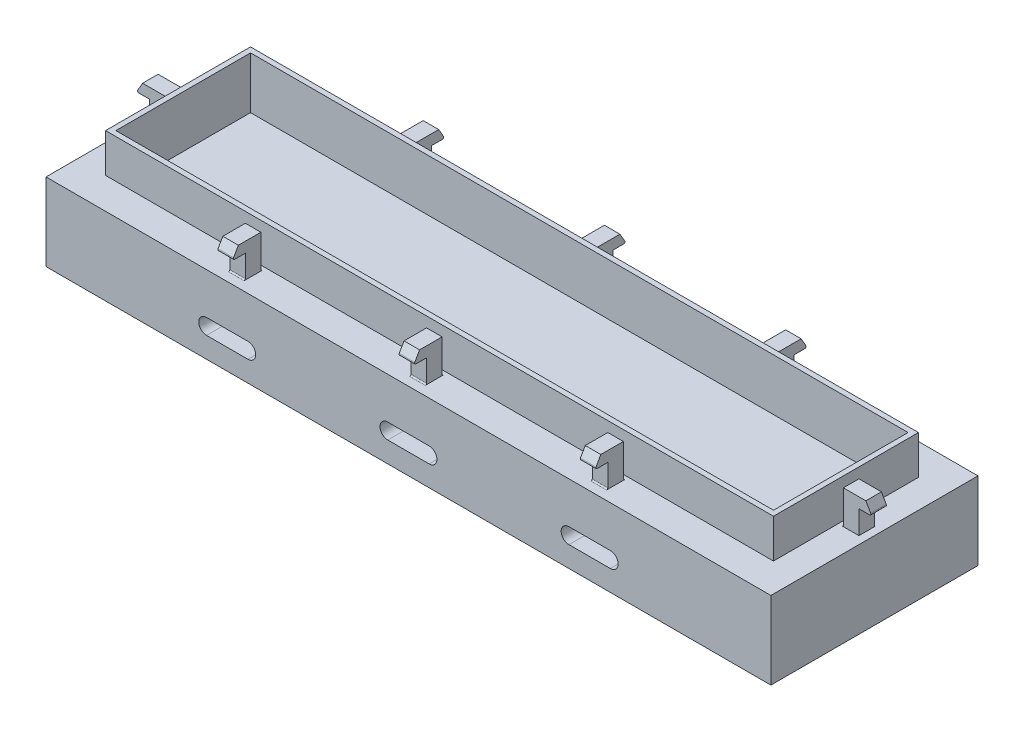
SolidWorks part; units mm, degrees
ref_plane "Front Plane" through (0, 0, 0) normal (0, 0, 1) x (1, 0, 0)
ref_plane "Top Plane" through (0, 0, 0) normal (0, 1, 0) x (1, 0, 0)
ref_plane "Right Plane" through (0, 0, 0) normal (1, 0, 0) x (0, 0, -1)
sketch "Sketch1" plane through (0, 0, 0) normal (0, 1, 0) x (1, 0, 0)
  line L1 (-70, -20) -> (70, -20)
  line L2 (-70, -20) -> (-70, 20)
  line L3 (-70, 20) -> (70, 20)
  line L4 (70, -20) -> (70, 20)
  line L5 (-70, -20) -> (70, 20) construction
  line L6 (-70, 20) -> (70, -20) construction
  point P0 (0, 0)
  dimension "D1" = 40
  dimension "D2" = 140
extrude "Boss-Extrude1" add sketch "Sketch1" along normal blind 15
ref_plane "Plane1" through (-35, 0, 0) normal (1, 0, 0) x (0, 0, -1)
sketch "Sketch3" plane through (0, 0, 0) normal (0, 0, 1) x (1, 0, 0)
  line L0 (-65.5, 15) -> (-65.5, 21.5)
  line L1 (-65.5, 21.5) -> (-69.8453, 21.5)
  line L2 (-69.8453, 21.5) -> (-71, 19.5)
  line L3 (-71, 19.5) -> (-68.5, 19.5)
  line L4 (-68.5, 19.5) -> (-68.5, 15)
  line L5 (-68.5, 15) -> (-65.5, 15)
  line L7 (-70, 15) -> (70, 15) construction
  line L8 (-70, 15) -> (-70, 0) construction
  dimension "D1" = 3
  dimension "D2" = 2.5
  dimension "D3" = 6.5
  dimension "D4" = 4.5
  dimension "D5" = 60
  dimension "D6" = 1.5
sketch "Sketch6" plane through (0, 0, 0) normal (1, 0, 0) x (0, 0, -1)
  line L0 (-15, 15) -> (-15, 21.5)
  line L1 (-15, 21.5) -> (-19.3453, 21.5)
  line L2 (-19.3453, 21.5) -> (-20.5, 19.5)
  line L3 (-20.5, 19.5) -> (-18, 19.5)
  line L4 (-18, 19.5) -> (-18, 15)
  line L5 (-18, 15) -> (-15, 15)
  line L6 (-20, 15) -> (20, 15) construction
  line L7 (-20, 15) -> (-20, 0) construction
  dimension "D1" = 3
  dimension "D2" = 2.5
  dimension "D3" = 6.5
  dimension "D4" = 4.5
  dimension "D5" = 60
  dimension "D6" = 2
sketch "Sketch7" plane through (-35, 0, 0) normal (1, 0, 0) x (0, 0, -1)
  line L0 (-15, 15) -> (-15, 21.5)
  line L1 (-15, 21.5) -> (-19.3453, 21.5)
  line L2 (-19.3453, 21.5) -> (-20.5, 19.5)
  line L3 (-20.5, 19.5) -> (-18, 19.5)
  line L4 (-18, 19.5) -> (-18, 15)
  line L5 (-18, 15) -> (-15, 15)
  line L6 (-20, 15) -> (20, 15) construction
  line L7 (-20, 15) -> (-20, 0) construction
  dimension "D1" = 3
  dimension "D2" = 2.5
  dimension "D3" = 6.5
  dimension "D4" = 4.5
  dimension "D5" = 60
  dimension "D6" = 2
extrude "Boss-Extrude2" add sketch "Sketch3" along normal blind 1.5 and the other way blind 1.5
extrude "Boss-Extrude3" add sketch "Sketch6" against normal blind 1.5
extrude "Boss-Extrude4" add sketch "Sketch7" along normal blind 1.5 and the other way blind 1.5
fillet "Fillet2" radius 0.25 1 edges at (-71, 19.5, 0)
mirror "Mirror9" about plane through (0, 0, 0) normal (1, 0, 0) of "Boss-Extrude3"
mirror "Mirror10" about plane through (0, 0, 0) normal (0, 0, 1) of "Boss-Extrude4", "Mirror9", "Boss-Extrude3"
mirror "Mirror11" about plane through (0, 0, 0) normal (1, 0, 0) of "Boss-Extrude2", "Mirror10", "Boss-Extrude4"
sketch "Sketch2" plane through (0, 15, 0) normal (0, 1, 0) x (1, 0, 0)
  line L1 (-64.5, -14) -> (64.5, -14)
  line L2 (-64.5, -14) -> (-64.5, 14)
  line L3 (-64.5, 14) -> (64.5, 14)
  line L4 (64.5, -14) -> (64.5, 14)
  line L5 (-64.5, -14) -> (64.5, 14) construction
  line L6 (-64.5, 14) -> (64.5, -14) construction
  line L8 (1.5, 15) -> (-1.5, 15) construction
  line L9 (-65.5, 1.5) -> (-65.5, -1.5) construction
  point P0 (0, 0)
  dimension "D1" = 1
  dimension "D2" = 1
extrude "Boss-Extrude5" add sketch "Sketch2" along normal blind 7.5
sketch "Sketch8" plane through (0, 22.5, 0) normal (0, 1, 0) x (1, 0, 0)
  line L0 (64.5, 14) -> (-64.5, 14) construction
  line L1 (-63.5, -13) -> (63.5, -13)
  line L2 (-63.5, -13) -> (-63.5, 13)
  line L3 (-63.5, 13) -> (63.5, 13)
  line L4 (63.5, -13) -> (63.5, 13)
  line L5 (-63.5, -13) -> (63.5, 13) construction
  line L6 (-63.5, 13) -> (63.5, -13) construction
  line L7 (-64.5, 14) -> (-64.5, -14) construction
  point P0 (0, 0)
  point P8 (0, 14)
  point P11 (-64.5, 0)
  dimension "D1" = 1
  dimension "D2" = 1
extrude "Cut-Extrude1" cut sketch "Sketch8" against normal blind 10
sketch "Sketch9" plane through (0, 0, 20) normal (0, 0, 1) x (1, 0, 0)
  line L0 (-4, 5.5) -> (4, 5.5) construction
  line L1 (-4, 7) -> (4, 7)
  line L2 (-4, 4) -> (4, 4)
  arc A0 (-4, 7) -> (-4, 4) centre (-4, 5.5) ccw
  arc A1 (4, 4) -> (4, 7) centre (4, 5.5) ccw
  point P2 (0, 5.5)
  dimension "D1" = 5.5
  dimension "D2" = 8
  dimension "D3" = 3
sketch "Sketch10" plane through (0, 0, 20) normal (0, 0, 1) x (1, 0, 0)
  line L0 (-39, 5.5) -> (-31, 5.5) construction
  line L1 (-39, 7) -> (-31, 7)
  line L2 (-39, 4) -> (-31, 4)
  line L3 (-35, -12.375) -> (-35, 12.375) construction
  line L5 (28.6787, 0) -> (-28.6787, 0) construction
  arc A0 (-39, 7) -> (-39, 4) centre (-39, 5.5) ccw
  arc A1 (-31, 4) -> (-31, 7) centre (-31, 5.5) ccw
  point P2 (-35, 5.5)
  dimension "D1" = 8
  dimension "D2" = 3
  dimension "D3" = 5.5
extrude "Cut-Extrude2" cut sketch "Sketch9" against normal through all
extrude "Cut-Extrude3" cut sketch "Sketch10" against normal through all
mirror "Mirror12" about plane through (0, 0, 0) normal (1, 0, 0) of "Cut-Extrude3"
fillet "Fillet3" radius 0.25 7 edges at (35, 19.5, -20.5) (0, 19.5, -20.5) (-35, 19.5, -20.5) (71, 19.5, 0) (35, 19.5, 20.5) (0, 19.5, 20.5) (-35, 19.5, 20.5)
fillet "Fillet4" radius 0.25 15 edges at (35, 15, 18) (0, 15, 18) (-35, 15, 18) (-68.5, 15, 0) (-35, 15, -18) (0, 15, -18) (35, 15, -18) (-65.5, 15, 0) (35, 15, -15) (0, 15, -15) (-35, 15, -15) (65.5, 15, 0) (-35, 15, 15) (35, 15, 15) (0, 15, 15)
